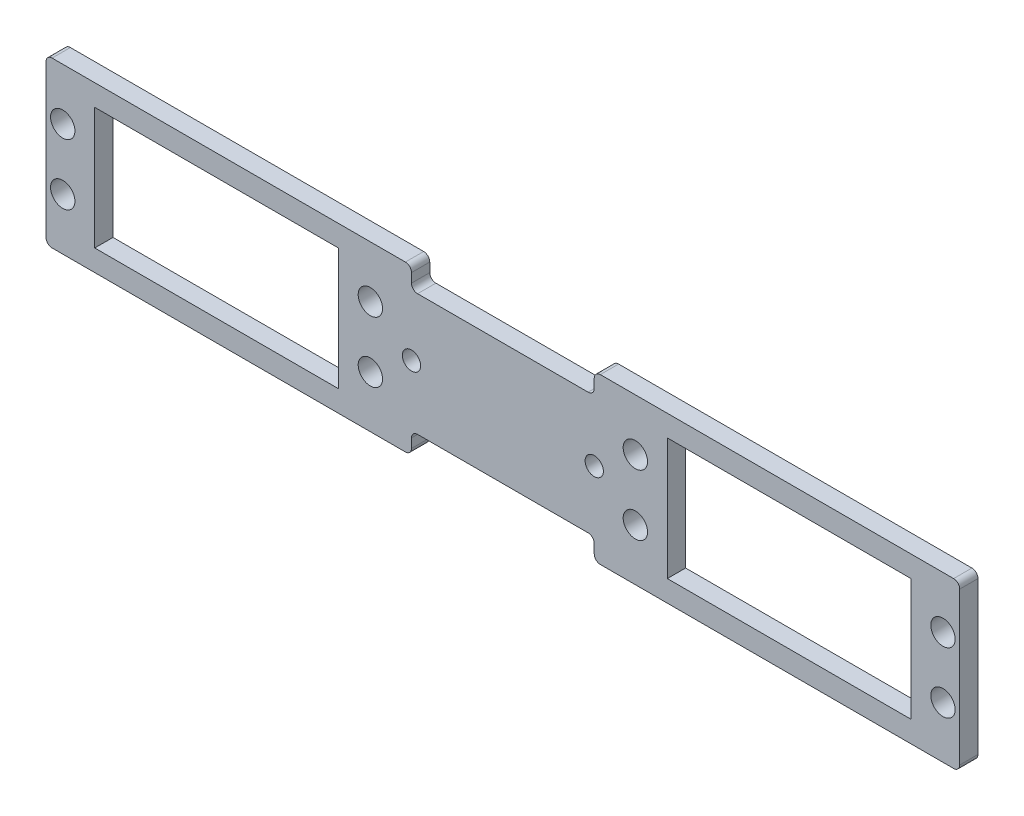
SolidWorks part; units mm, degrees
ref_plane "Alzado" through (0, 0, 0) normal (0, 0, 1) x (1, 0, 0)
ref_plane "Planta" through (0, 0, 0) normal (0, 1, 0) x (1, 0, 0)
ref_plane "Vista lateral" through (0, 0, 0) normal (1, 0, 0) x (0, 0, -1)
sketch "Croquis1" plane through (0, 0, 0) normal (0, 0, 1) x (1, 0, 0)
  line L0 (-15, 13.5) -> (-15, -13.5) construction
  line L1 (75, 13.5) -> (15, 13.5)
  line L2 (75, 13.5) -> (75, -13.5)
  line L3 (75, -13.5) -> (15, -13.5)
  line L4 (-75, 13.5) -> (-75, -13.5)
  line L5 (75, 13.5) -> (-75, -13.5) construction
  line L6 (75, -13.5) -> (-75, 13.5) construction
  line L7 (15, 10) -> (-15, 10)
  line L8 (15, 10) -> (15, -10) construction
  line L9 (15, -10) -> (-15, -10)
  line L10 (-15, 10) -> (-15, -10) construction
  line L11 (15, 10) -> (-15, -10) construction
  line L12 (15, -10) -> (-15, 10) construction
  line L13 (15, 13.5) -> (15, -13.5) construction
  line L14 (-15, 13.5) -> (-75, 13.5)
  line L15 (-15, -13.5) -> (-75, -13.5)
  line L16 (-15, -13.5) -> (-15, -10)
  line L17 (-15, 10) -> (-15, 13.5)
  line L18 (15, 13.5) -> (15, 10)
  line L19 (15, -10) -> (15, -13.5)
  point P0 (0, 0)
  point P6 (0, 0)
  dimension "D1" = 27
  dimension "D2" = 150
  dimension "D3" = 30
  dimension "D4" = 20
extrude "Saliente-Extruir1" add sketch "Croquis1" along normal blind 3
sketch "Croquis2" plane through (0, 0, 3) normal (0, 0, 1) x (1, 0, 0)
  line L0 (-19.25, 10) -> (-74.75, 10)
  line L1 (-19.25, 10) -> (-19.25, -10)
  line L2 (-19.25, -10) -> (-74.75, -10)
  line L3 (-74.75, 10) -> (-74.75, -10)
  line L4 (-19.25, 10) -> (-74.75, -10) construction
  line L5 (-19.25, -10) -> (-74.75, 10) construction
  line L6 (-47, 0) -> (-67, 0) construction
  line L9 (-75, 0) -> (-67, 0) construction
  line L10 (-75, 13.5) -> (-75, -13.5) construction
  circle A0 centre (-72.25, 5) radius 2
  circle A1 centre (-72.25, -5) radius 2
  circle A2 centre (-21.75, 5) radius 2
  circle A3 centre (-21.75, -5) radius 2
  point P0 (-47, 0)
  dimension "D1" = 8
  dimension "D2" = 20
sketch "Croquis3" plane through (0, 0, 3) normal (0, 0, 1) x (1, 0, 0)
  line L0 (-19.25, 10) -> (-74.75, 10) construction
  line L1 (-27, 10) -> (-67, 10)
  line L2 (-27, 10) -> (-27, -10)
  line L3 (-27, -10) -> (-67, -10)
  line L4 (-67, 10) -> (-67, -10)
  line L5 (-27, 10) -> (-67, -10) construction
  line L6 (-27, -10) -> (-67, 10) construction
  line L7 (0, 10) -> (0, -10) construction
  line L8 (15, 10) -> (-15, 10) construction
  line L9 (-15, -10) -> (15, -10) construction
  line L10 (27, -10) -> (67, 10) construction
  line L11 (27, 10) -> (67, -10) construction
  line L12 (67, 10) -> (67, -10)
  line L13 (27, -10) -> (67, -10)
  line L14 (27, 10) -> (27, -10)
  line L15 (27, 10) -> (67, 10)
  circle A0 centre (-21.75, -5) radius 2 construction
  circle A1 centre (-21.75, 5) radius 2 construction
  circle A2 centre (-72.25, -5) radius 2 construction
  circle A3 centre (-72.25, 5) radius 2 construction
  circle A4 centre (-21.75, -5) radius 2
  circle A5 centre (-21.75, 5) radius 2
  circle A6 centre (-72.25, -5) radius 2
  circle A7 centre (-72.25, 5) radius 2
  circle A8 centre (72.25, 5) radius 2
  circle A9 centre (72.25, -5) radius 2
  circle A10 centre (21.75, 5) radius 2
  circle A11 centre (21.75, -5) radius 2
  point P0 (-47, 0)
  point P39 (47, 0)
extrude "Cortar-Extruir1" cut sketch "Croquis3" against normal through all
fillet "Redondeo1" radius 1 12 edges at (-75, 13.5, 1.5) (-15, 13.5, 1.5) (-15, 10, 1.5) (15, 10, 1.5) (15, 13.5, 1.5) (75, 13.5, 1.5) (75, -13.5, 1.5) (15, -13.5, 1.5) (15, -10, 1.5) (-15, -10, 1.5) (-15, -13.5, 1.5) (-75, -13.5, 1.5)
sketch "Croquis4" plane through (0, 0, 3) normal (0, 0, 1) x (1, 0, 0)
  line L0 (15, 0) -> (-15, 0) construction
  line L1 (75, -12.5) -> (75, 12.5) construction
  line L4 (-47, 0) -> (-67, 0) construction
  line L5 (-74.75, 10) -> (-74.75, -10) construction
  circle A0 centre (15, 0) radius 1.5
  circle A1 centre (-15, 0) radius 1.5
  point P4 (-56.75, 0)
  point P8 (0, 0)
  point P12 (57, 0)
  point P15 (0, 0)
  dimension "D3" = 3
  dimension "D1" = 18
  dimension "D2" = 41.75
  dimension "D4" = 30
  dimension "D5" = 18
  dimension "D6" = 113.75
extrude "Cortar-Extruir2" cut sketch "Croquis4" against normal blind 3
